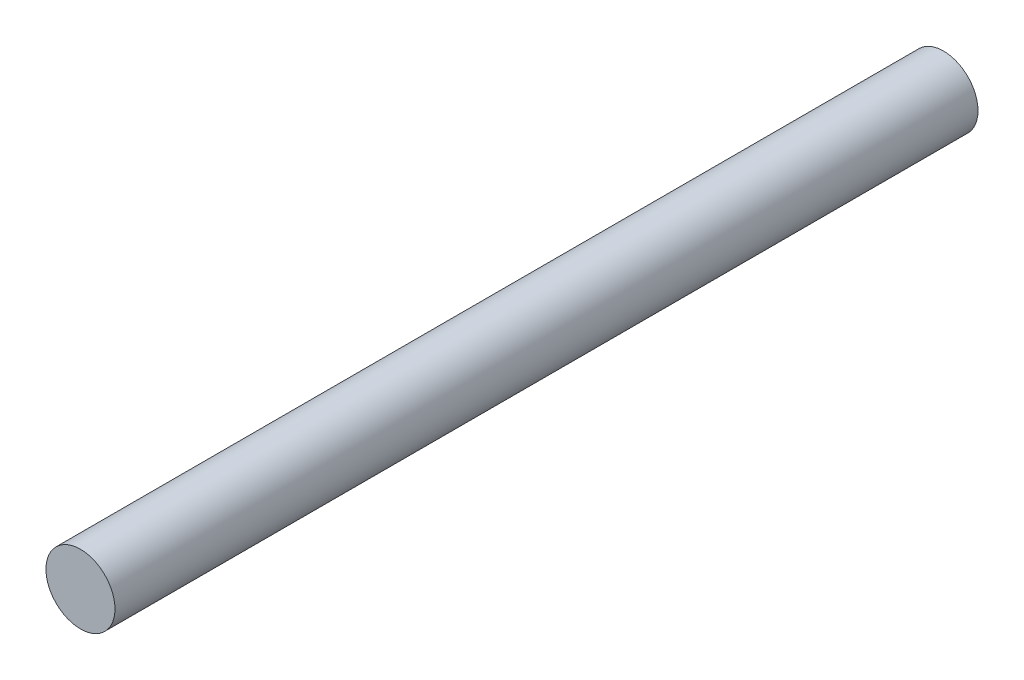
SolidWorks part; units mm, degrees
ref_plane "Front Plane" through (0, 0, 0) normal (0, 0, 1) x (1, 0, 0)
ref_plane "Top Plane" through (0, 0, 0) normal (0, 1, 0) x (1, 0, 0)
ref_plane "Right Plane" through (0, 0, 0) normal (1, 0, 0) x (0, 0, -1)
sketch "Sketch1" plane through (0, 0, 0) normal (0, 0, 1) x (1, 0, 0)
  circle A0 centre (0, 0) radius 5
  dimension "D1" = 10
extrude "Boss-Extrude1" add sketch "Sketch1" along normal blind 125
